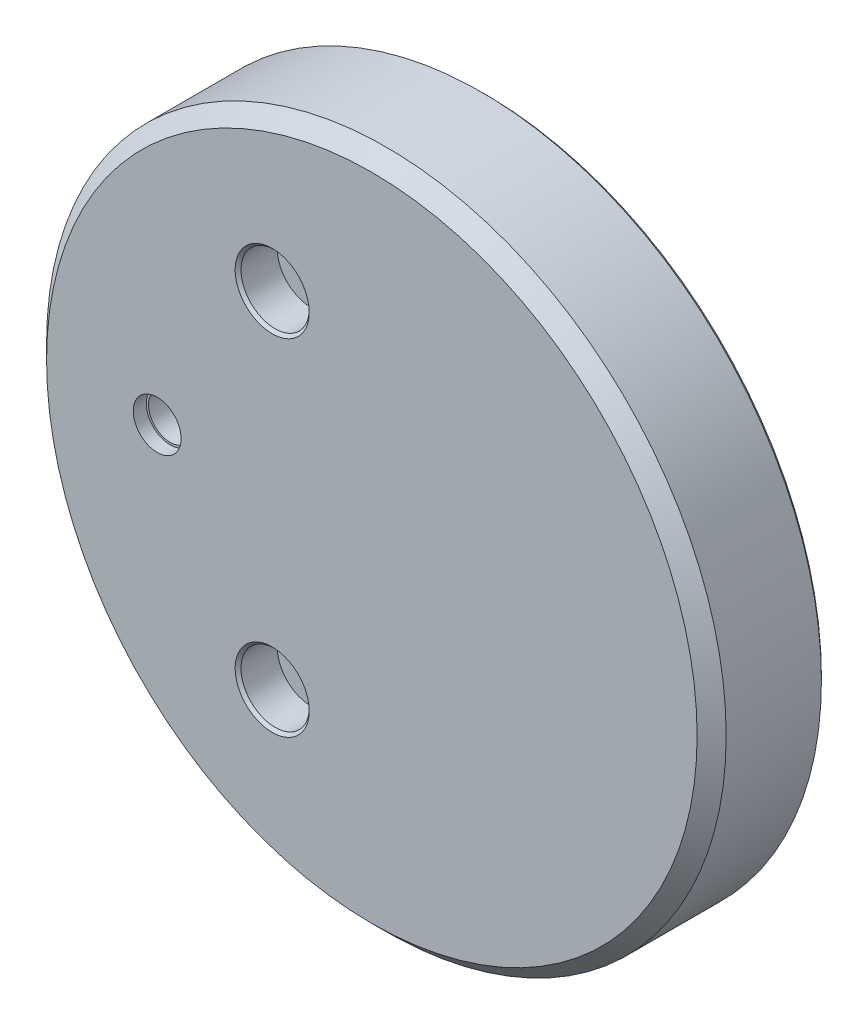
SolidWorks part; units mm, degrees
material "玻璃"
ref_plane "前视基准面" through (0, 0, 0) normal (0, 0, 1) x (1, 0, 0)
ref_plane "上视基准面" through (0, 0, 0) normal (0, 1, 0) x (1, 0, 0)
ref_plane "右视基准面" through (0, 0, 0) normal (1, 0, 0) x (0, 0, -1)
sketch "草图1" plane through (0, 0, 0) normal (0, 0, 1) x (1, 0, 0)
  line L0 (111.6566, 115.826) -> (112.2591, 115.826)
  line L1 (97.4417, 80.774) -> (97.5378, 80.774)
  line L2 (96.3948, 81.4616) -> (96.3948, 88.14)
  line L3 (94.9171, 90.6338) -> (95.6764, 89.8744)
  line L4 (83.1868, 91.442) -> (92.9658, 91.442)
  line L5 (81.9168, 92.712) -> (81.9168, 102.618)
  line L6 (83.1868, 103.888) -> (94.4898, 103.888)
  line L7 (95.7598, 105.158) -> (95.7598, 109.857)
  line L8 (95.7598, 109.857) -> (95.7598, 115.064)
  line L9 (97.5995, 115.826) -> (111.6566, 115.826)
  line L10 (115.5855, 112.8877) -> (117.729, 110.744)
  line L13 (118.618, 91.8212) -> (118.618, 108.839)
  line L14 (112.9575, 85.0176) -> (117.8116, 89.8718)
  line L15 (103.8878, 84.457) -> (111.604, 84.457)
  line L16 (103.1258, 81.663) -> (103.1258, 83.695)
  line L17 (101.7724, 80.774) -> (102.2368, 80.774)
  line L18 (97.4417, 80.774) -> (101.7724, 80.774)
  line L19 (97.5995, 115.826) -> (96.6877, 115.826)
  line L20 (118.618, 109.4605) -> (118.618, 108.839)
  line L21 (117.729, 110.744) -> (118.3394, 110.1099)
  arc A0 (112.9575, 85.0176) -> (111.604, 84.457) centre (111.604, 86.3711) cw
  arc A1 (96.6877, 115.826) -> (95.7598, 115.064) centre (96.6877, 114.8802) ccw
  arc A2 (118.3394, 110.1099) -> (118.618, 109.4605) centre (117.6188, 109.4163) cw
  arc A38 (112.9419, 115.5406) -> (112.2591, 115.826) centre (112.2555, 114.8581) ccw
  arc A41 (115.5855, 112.8877) -> (112.9419, 115.5406) centre (100.0001, 100.0001) ccw
  arc A44 (96.5218, 81.155) -> (97.4417, 80.774) centre (97.4417, 82.0748) ccw
  arc A47 (96.3948, 81.4616) -> (96.5218, 81.155) centre (96.8285, 81.4616) ccw
  arc A50 (96.3948, 88.14) -> (95.6764, 89.8744) centre (93.942, 88.14) ccw
  arc A53 (94.9171, 90.6338) -> (92.9658, 91.442) centre (92.9658, 88.6826) ccw
  arc A56 (81.9168, 92.712) -> (83.1868, 91.442) centre (83.1868, 92.712) ccw
  arc A59 (83.1868, 103.888) -> (81.9168, 102.618) centre (83.1868, 102.618) ccw
  arc A62 (94.4898, 103.888) -> (95.7598, 105.158) centre (94.4898, 105.158) ccw
  arc A71 (117.8116, 89.8718) -> (118.618, 91.8212) centre (115.8586, 91.8212) ccw
  arc A80 (103.8878, 84.457) -> (103.1258, 83.695) centre (103.8878, 83.695) ccw
  arc A83 (102.2368, 80.774) -> (103.1258, 81.663) centre (102.2368, 81.663) ccw
sketch "草图2" plane through (0, 0, 0) normal (0, 0, 1) x (1, 0, 0)
  circle A0 centre (100.0001, 100.0001) radius 21.6
sketch "草图3" plane through (0, 0, 0) normal (0, 0, 1) x (1, 0, 0)
  circle A0 centre (100.0001, 100.0001) radius 23.4
extrude "凸台-拉伸1" add sketch "草图3" along normal blind 7.81
extrude "切除-拉伸1" cut sketch "草图2" along normal blind 2.1
extrude "切除-拉伸2" cut sketch "草图1" along normal blind 3.2 from surface at 2.1
sketch "草图4" plane through (0, 0, 0) normal (0, 0, 1) x (1, 0, 0)
  circle A0 centre (85.217, 99.949) radius 1.5
  circle A3 centre (93.1375, 88.1138) radius 1.25
  circle A6 centre (93.1375, 111.8862) radius 1.25
extrude "切除-拉伸5" cut sketch "草图4" along direction (0, 0, 1) on the side against the normal up to next from surface at 7.81
sketch "草图5" plane through (0, 0, 0) normal (0, 0, 1) x (1, 0, 0)
  circle A0 centre (85.217, 99.949) radius 1.65
extrude "切除-拉伸6" cut sketch "草图5" against normal blind 0.9 from surface at 7.81 starting at face at (94.3875, 111.8862, 7.81)
sketch "草图6" plane through (0, 0, 0) normal (0, 0, 1) x (1, 0, 0)
  circle A0 centre (93.1375, 111.8862) radius 2.35
  circle A1 centre (93.1375, 88.1138) radius 2.35
extrude "切除-拉伸7" cut sketch "草图6" against normal blind 2.7 from surface at 7.81 starting at face at (86.867, 99.949, 7.81)
sketch "草图7" plane through (0, 0, 0) normal (0, 0, 1) x (1, 0, 0)
  circle A0 centre (100.0187, 99.9448) radius 3.2
extrude "切除-拉伸8" cut sketch "草图7" along normal blind 1 from surface at 5.3 starting at face at (86.717, 99.949, 5.3)
chamfer "倒角1" distance 1 angle 45 1 edges at (123.4001, 100.0001, 7.81)
chamfer "倒角2" distance 0.25 angle 45 2 edges at (121.6001, 100.0001, 0) (123.4001, 100.0001, 0)
chamfer "倒角3" distance 0.2 angle 45 3 edges at (103.2187, 99.9448, 5.3) (95.4875, 88.1138, 7.81) (95.4875, 111.8862, 7.81)
